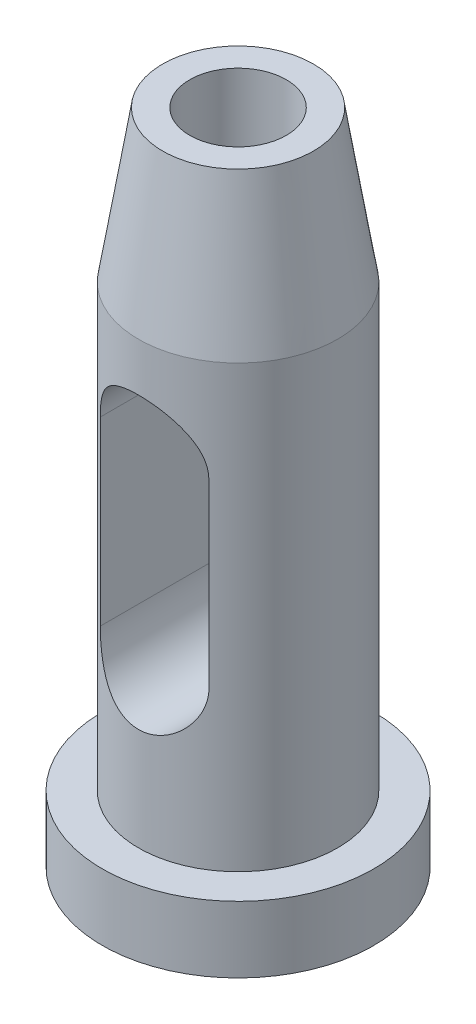
SolidWorks part; units mm, degrees
ref_plane "Front Plane" through (0, 0, 0) normal (0, 0, 1) x (1, 0, 0)
ref_plane "Top Plane" through (0, 0, 0) normal (0, 1, 0) x (1, 0, 0)
ref_plane "Right Plane" through (0, 0, 0) normal (1, 0, 0) x (0, 0, -1)
sketch "Sketch1" plane through (0, 0, 0) normal (0, 0, 1) x (1, 0, 0)
  line L0 (0, 0) -> (22.5, 0)
  line L1 (22.5, 0) -> (22.5, 11)
  line L2 (22.5, 11) -> (16.5, 11)
  line L3 (16.5, 11) -> (16.5, 84)
  line L4 (0, 0) -> (0, 151.2872) construction
  line L5 (0, 109) -> (12.5, 109)
  line L6 (12.5, 109) -> (16.5, 84)
  line L7 (0, 0) -> (0, 109)
  dimension "D1" = 22.5
  dimension "D2" = 16.5
  dimension "D3" = 11
  dimension "D4" = 109
  dimension "D5" = 12.5
  dimension "D6" = 25
revolve "Revolve1" add sketch "Sketch1" angle 360 about L4
sketch "Sketch2" plane through (0, 0, 0) normal (0, 0, 1) x (1, 0, 0)
  line L0 (0, 67) -> (0, 37) construction
  line L1 (9, 67) -> (9, 37)
  line L2 (-9, 67) -> (-9, 37)
  line L3 (22.5, 11) -> (-22.5, 11) construction
  arc A0 (9, 67) -> (-9, 67) centre (0, 67) ccw
  arc A1 (-9, 37) -> (9, 37) centre (0, 37) ccw
  point P2 (0, 52)
  point P9 (0, 0)
  dimension "D2" = 9
  dimension "D1" = 26
  dimension "D3" = 30
extrude "Cut-Extrude1" cut sketch "Sketch2" against normal through all both and the other way through all
sketch "Sketch3" plane through (0, 109, 0) normal (0, 1, 0) x (1, 0, 0)
  circle A0 centre (0, 0) radius 8
  dimension "D1" = 16
extrude "Cut-Extrude2" cut sketch "Sketch3" against normal up to next
